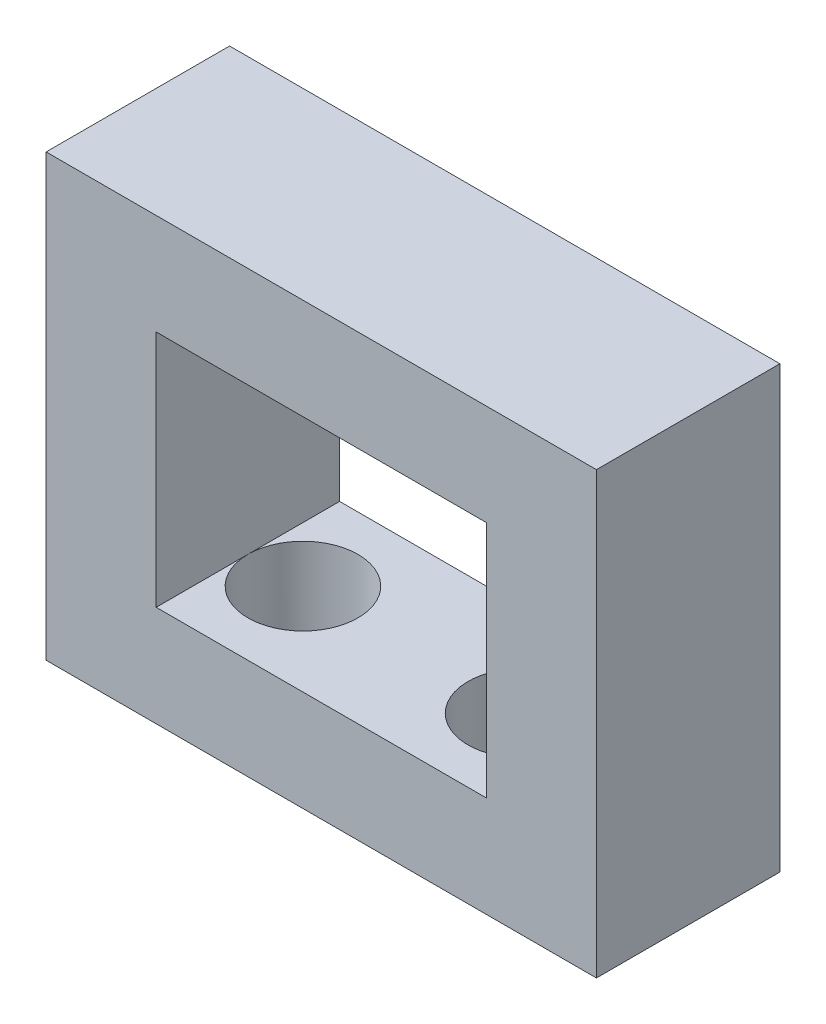
SolidWorks part; units mm, degrees
material "ABS"
ref_plane "前基準面" through (0, 0, 0) normal (0, 0, 1) x (1, 0, 0)
ref_plane "上基準面" through (0, 0, 0) normal (0, 1, 0) x (1, 0, 0)
ref_plane "右基準面" through (0, 0, 0) normal (1, 0, 0) x (0, 0, -1)
sketch "草圖1" plane through (0, 0, 0) normal (0, 0, 1) x (1, 0, 0)
  line L1 (-7.5, -6) -> (7.5, -6)
  line L2 (-7.5, -6) -> (-7.5, 6)
  line L3 (-7.5, 6) -> (7.5, 6)
  line L4 (7.5, -6) -> (7.5, 6)
  line L5 (-7.5, -6) -> (7.5, 6) construction
  line L6 (-7.5, 6) -> (7.5, -6) construction
  point P0 (0, 0)
  dimension "D1" = 15
  dimension "D2" = 12
extrude "填料-伸長1" add sketch "草圖1" along normal mid plane 5
sketch "草圖2" plane through (0, 0, 2.5) normal (0, 0, 1) x (1, 0, 0)
  line L1 (-4.5, -3.25) -> (4.5, -3.25)
  line L2 (-4.5, -3.25) -> (-4.5, 3.25)
  line L3 (-4.5, 3.25) -> (4.5, 3.25)
  line L4 (4.5, -3.25) -> (4.5, 3.25)
  line L5 (-4.5, -3.25) -> (4.5, 3.25) construction
  line L6 (-4.5, 3.25) -> (4.5, -3.25) construction
  point P0 (0, 0)
  dimension "D1" = 9
  dimension "D2" = 6.5
extrude "除料-伸長1" cut sketch "草圖2" against normal through all
sketch "草圖3" plane through (0, -6, 0) normal (0, -1, 0) x (1, 0, 0)
  line L0 (-3, 0) -> (3, 0) construction
  circle A0 centre (-3, 0) radius 1.5
  circle A1 centre (3, 0) radius 1.5
  point P4 (0, 0)
  dimension "D1" = 3
  dimension "D2" = 6
extrude "除料-伸長2" cut sketch "草圖3" against normal up to next
